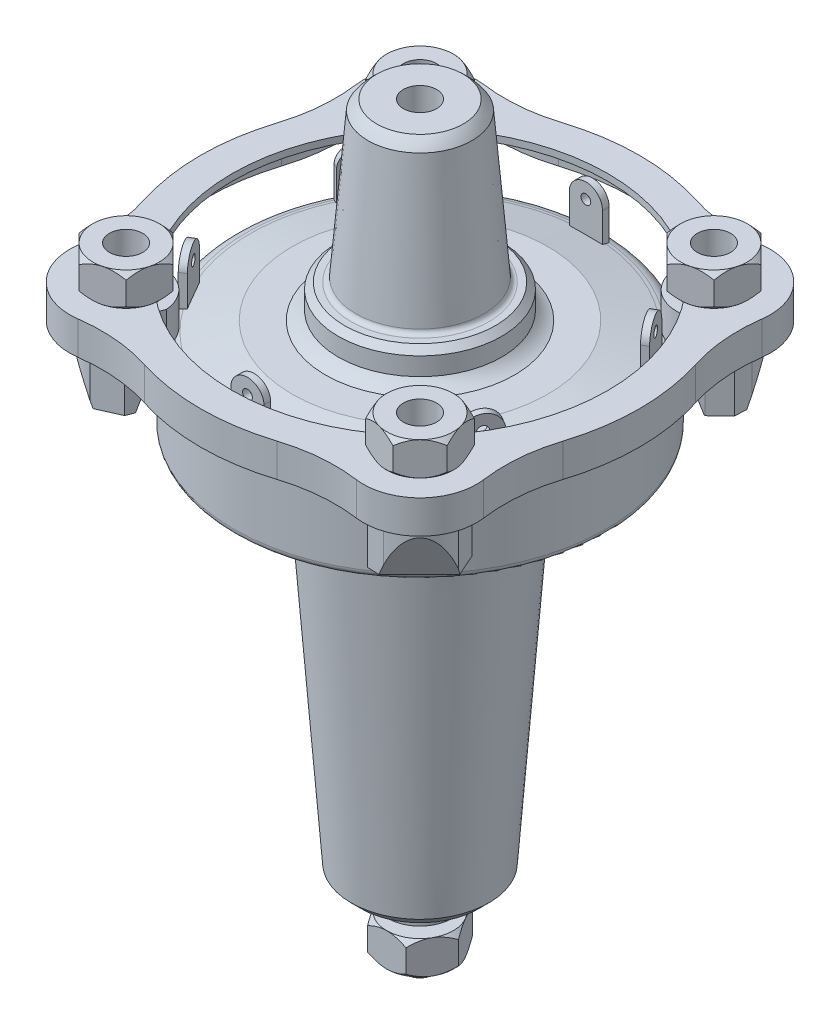
SolidWorks part; units mm, degrees
ref_plane "Front Plane" through (0, 0, 0) normal (0, 0, 1) x (1, 0, 0)
ref_plane "Top Plane" through (0, 0, 0) normal (0, 1, 0) x (1, 0, 0)
ref_plane "Right Plane" through (0, 0, 0) normal (1, 0, 0) x (0, 0, -1)
sketch "Sketch1" plane through (0, 0, 0) normal (0, 0, 1) x (1, 0, 0)
  line L0 (0, 166.4746) -> (0, -166.4746) construction
  line L1 (-56, 2.0022) -> (-56, 20.3181)
  line L2 (-28.0132, -12.6366) -> (-20.7003, -113)
  line L3 (-17.7003, -116) -> (0, -116)
  line L4 (-5.0055, -122.5803) -> (-9.6428, -122.5803) construction
  line L5 (-5.0055, -136) -> (-5.0055, -122.5803) construction
  line L6 (-2.0055, -139) -> (-5.0055, -136) construction
  line L7 (0.0742, -139) -> (-2.0055, -139) construction
  line L8 (-9.6428, -122.5803) -> (-9.6428, -116) construction
  line L9 (-20.7003, -113) -> (-17.7003, -116)
  line L10 (-54.1689, 0) -> (-40.2943, 0)
  line L11 (-38, -8) -> (-33, -8)
  line L12 (-38, -2.0022) -> (-38, -8)
  line L13 (-13.0055, 86) -> (-5.0055, 86)
  line L14 (-19.2424, 39.6846) -> (-15.6526, 83)
  line L15 (-52.1261, 25.194) -> (-51.0561, 25.4408)
  line L16 (-51.0561, 25.4408) -> (-38.4491, 28.3512)
  line L17 (-24.5676, 36.4753) -> (-22.7003, 38.3425)
  line L18 (-38.4491, 28.3512) -> (-28.4491, 28.3512)
  line L19 (-24.5676, 31.062) -> (-24.5676, 36.4753)
  line L20 (-22.7003, 38.3425) -> (-20.7003, 38.3425)
  line L21 (-40.2943, 0) -> (0, 0) construction
  line L22 (-5.0055, -116) -> (-5.0055, 86)
  arc A0 (-38, -2.0022) -> (-40.2943, 0) centre (-40.0021, -1.9808) ccw
  arc A1 (-56, 2.0022) -> (-54.1689, 0) centre (-53.9978, 1.9949) ccw
  arc A2 (-28.0132, -12.6366) -> (-33, -8) centre (-33, -13) ccw
  arc A3 (-52.1261, 25.194) -> (-56, 20.3181) centre (-50.9945, 20.3181) ccw
  arc A4 (-28.4491, 28.3512) -> (-24.5676, 31.062) centre (-31.6492, 37.0674) ccw
  arc A5 (-20.7003, 38.3425) -> (-19.2424, 39.6846) centre (-20.7003, 39.8055) ccw
  arc A6 (-13.0055, 86) -> (-15.6526, 83) centre (-3.4278, 74.881) ccw
  dimension "D11" = 5
  dimension "D13" = 3
  dimension "D16" = 1.4629
  dimension "D20" = 9.2851
  dimension "D1" = 225
  dimension "D2" = 108
  dimension "D3" = 15.6526
  dimension "D4" = 5.0055
  dimension "D5" = 28.3512
  dimension "D6" = 38
  dimension "D7" = 56
  dimension "D8" = 8
  dimension "D9" = 86
  dimension "D10" = 5
  dimension "D12" = 8
  dimension "D14" = 6.5803
  dimension "D15" = 2
  dimension "D17" = 3
  dimension "D18" = 3
  dimension "D19" = 10
  dimension "D21" = 39.6846
  dimension "D22" = 3
  dimension "D23" = 3
revolve "Revolve1" add sketch "Sketch1" angle 360 about L0
sketch "Sketch2" plane through (0, 0, 0) normal (0, 0, 1) x (1, 0, 0)
  line L0 (-9.6428, -116) -> (-9.6428, -122.5803)
  line L1 (-9.6428, -122.5803) -> (-5.0055, -122.5803)
  line L2 (-5.0055, -122.5803) -> (-5.0055, -136)
  line L3 (-5.0055, -136) -> (-4.0044, -140.0739)
  line L4 (-4.0044, -140.0739) -> (0, -140.0739)
  line L5 (0, -140.0739) -> (0, -116)
  line L6 (-9.6428, -116) -> (0, -116)
  line L7 (-17.7003, -116) -> (17.7003, -116) construction
  dimension "D1" = 24.0739
revolve "Revolve2" add sketch "Sketch2" angle 360 about L0
sketch "Sketch3" plane through (0, 28.3512, 0) normal (0, 1, 0) x (1, 0, 0)
  line L0 (0, 0) -> (-54.025, 54.025) construction
  line L1 (0, 0) -> (0, 76.5481) construction
  line L2 (-40.52, 47.5855) -> (-36.6301, 43.0173)
  line L3 (-47.5855, 40.52) -> (-43.3277, 36.2623)
  line L4 (80.1584, 0) -> (-80.1584, 0) construction
  line L5 (-47.5855, -40.52) -> (-43.3277, -36.2623)
  line L6 (-40.52, -47.5855) -> (-36.6301, -43.0173)
  line L7 (0, 0) -> (54.025, 54.025) construction
  line L8 (40.52, -47.5855) -> (36.6301, -43.0173)
  line L9 (47.5855, -40.52) -> (43.3277, -36.2623)
  line L10 (47.5855, 40.52) -> (43.3277, 36.2623)
  line L11 (40.52, 47.5855) -> (36.6301, 43.0173)
  arc A0 (-62.9108, 19.9557) -> (-62.9108, -19.9557) centre (0, 0) ccw
  arc A1 (-43.3277, 36.2623) -> (-43.3277, -36.2623) centre (0, 0) ccw
  arc A2 (62.5, 0) -> (-62.5, 0) centre (0, 0) ccw construction
  arc A3 (-40.52, 47.5855) -> (-47.5855, 40.52) centre (-44.1942, 44.1942) ccw
  arc A4 (-41.88, 61.0359) -> (-61.0359, 41.88) centre (-44.1942, 44.1942) ccw
  circle A5 centre (-44.1942, 44.1942) radius 5 construction
  circle A6 centre (-44.1942, 44.1942) radius 17 construction
  arc A7 (19.9557, 62.9108) -> (-19.9557, 62.9108) centre (0, 0) ccw
  arc A8 (36.6301, 43.0173) -> (-36.6301, 43.0173) centre (0, 0) ccw
  arc A9 (-41.88, 61.0359) -> (-19.9557, 62.9108) centre (-35.0737, 110.5705) ccw
  arc A10 (-61.0359, 41.88) -> (-62.9108, 19.9557) centre (-110.5705, 35.0737) cw
  arc A11 (19.9557, -62.9108) -> (-19.9557, -62.9108) centre (0, 0) cw
  arc A12 (36.6301, -43.0173) -> (-36.6301, -43.0173) centre (0, 0) cw
  arc A13 (-61.0359, -41.88) -> (-62.9108, -19.9557) centre (-110.5705, -35.0737) ccw
  arc A14 (-41.88, -61.0359) -> (-19.9557, -62.9108) centre (-35.0737, -110.5705) cw
  arc A15 (-41.88, -61.0359) -> (-61.0359, -41.88) centre (-44.1942, -44.1942) cw
  arc A16 (-40.52, -47.5855) -> (-47.5855, -40.52) centre (-44.1942, -44.1942) cw
  arc A17 (40.52, -47.5855) -> (47.5855, -40.52) centre (44.1942, -44.1942) ccw
  arc A18 (41.88, -61.0359) -> (61.0359, -41.88) centre (44.1942, -44.1942) ccw
  arc A19 (41.88, -61.0359) -> (19.9557, -62.9108) centre (35.0737, -110.5705) ccw
  arc A20 (61.0359, -41.88) -> (62.9108, -19.9557) centre (110.5705, -35.0737) cw
  arc A21 (61.0359, 41.88) -> (62.9108, 19.9557) centre (110.5705, 35.0737) ccw
  arc A22 (41.88, 61.0359) -> (19.9557, 62.9108) centre (35.0737, 110.5705) cw
  arc A23 (41.88, 61.0359) -> (61.0359, 41.88) centre (44.1942, 44.1942) cw
  arc A24 (40.52, 47.5855) -> (47.5855, 40.52) centre (44.1942, 44.1942) cw
  arc A25 (43.3277, 36.2623) -> (43.3277, -36.2623) centre (0, 0) cw
  arc A26 (62.9108, 19.9557) -> (62.9108, -19.9557) centre (0, 0) cw
  dimension "D1" = 132
  dimension "D2" = 113
  dimension "D3" = 125
  dimension "D5" = 10
  dimension "D7" = 50
  dimension "D4" = 45
  dimension "D6" = 12
extrude "Boss-Extrude1" add sketch "Sketch3" along normal blind 10 separate body
shell "Shell1" thickness 2
sketch "Sketch5" plane through (0, 0, 0) normal (0, 1, 0) x (1, 0, 0)
  line L0 (-56.215, 56.215) -> (56.215, -56.215) construction
  arc A0 (-41.88, 61.0359) -> (-61.0359, 41.88) centre (-44.1942, 44.1942) ccw construction
  arc A1 (41.88, -61.0359) -> (61.0359, -41.88) centre (44.1942, -44.1942) ccw construction
ref_plane "Plane2" through (0, 0, 0) normal (-0.7071, 0, 0.7071) x (0.7071, 0, 0.7071)
sketch "Sketch6" plane through (0, 36.3512, 0) normal (0, -1, 0) x (1, 0, 0)
  line L0 (-44.4685, -55.424) -> (-39.4441, -55.1901)
  line L1 (-39.4441, -55.1901) -> (-35.0009, -50.6492)
  line L2 (-55.4219, -43.8429) -> (-52.2302, -36.6333)
  line L3 (-52.2302, -36.6333) -> (-43.2487, -33.0009)
  circle A0 centre (-44.1942, -44.1942) radius 6
  arc A1 (-35.0009, -50.6492) -> (-43.2487, -33.0009) centre (-44.1942, -44.1942) ccw
  arc A2 (-55.4219, -43.8429) -> (-44.4685, -55.424) centre (-44.1942, -44.1942) ccw
  line M17 (-47.5855, -40.52) -> (-43.3277, -36.2623)
  arc M18 (-43.3277, -36.2623) -> (-43.3277, 36.2623) centre (0, 0) cw
  arc M30 (36.6301, -43.0173) -> (-36.6301, -43.0173) centre (0, 0) cw
  line M31 (-36.6301, -43.0173) -> (-40.52, -47.5855)
  dimension "D1" = 12
extrude "Boss-Extrude2" add sketch "Sketch6" along normal blind 25 separate body contours L2 A2 L0 L1 A1 A0 L3 M30 M31 M17 M18 | A1 L3 A0 M30 M18 M17 M31
sketch "Sketch9" plane through (0, 0, 0) normal (-0.7071, 0, 0.7071) x (0.7071, 0, 0.7071)
  line L0 (-65.5502, -3.0446) -> (-56.4356, 22.8867)
  line L1 (-50.7439, 26.5641) -> (-50.7439, -3.0446)
  line L2 (-50.7439, -3.0446) -> (-65.5502, -3.0446)
  arc A0 (-56.4356, 22.8867) -> (-50.7439, 26.5641) centre (-51.1323, 20.9219) cw
extrude "Cut-Extrude1" cut sketch "Sketch9" against normal up to next and the other way up to next
sketch "Sketch18" plane through (0, 0, 0) normal (-0.7071, 0, 0.7071) x (0.7071, 0, 0.7071)
  line L0 (-73.7332, 23.8512) -> (-69.328, 10.7679)
  line L1 (-73.7332, 36.3512) -> (-73.7332, 11.3512) construction
  line L2 (-73.7332, 23.8512) -> (-73.7332, 10.7679)
  line L6 (-73.7332, 10.7679) -> (-69.328, 10.7679)
extrude "Cut-Extrude2" cut sketch "Sketch18" against normal blind 25 and the other way blind 25
sketch "Sketch11" plane through (0, 0, 0) normal (0, -1, 0) x (1, 0, 0)
  circle A0 centre (-44.1942, -44.1942) radius 5
  dimension "D1" = 10
extrude "Boss-Extrude4" add sketch "Sketch11" against normal blind 55 from offset 4 separate body
sketch "Sketch12" plane through (0, 38.3512, 0) normal (0, 1, 0) x (1, 0, 0)
  line L0 (-51.2652, 51.2652) -> (-37.1231, 37.1231) construction
  line L1 (-47.1828, 55.3477) -> (-55.3477, 47.1828)
  line L2 (-55.3477, 47.1828) -> (-52.3591, 36.0292)
  line L3 (-52.3591, 36.0292) -> (-41.2056, 33.0406)
  line L4 (-41.2056, 33.0406) -> (-33.0406, 41.2056)
  line L5 (-33.0406, 41.2056) -> (-36.0292, 52.3591)
  line L6 (-36.0292, 52.3591) -> (-47.1828, 55.3477)
  line L7 (-61.8365, 61.8365) -> (61.8365, -61.8365) construction
  circle A0 centre (-44.1942, 44.1942) radius 10 construction
  circle A1 centre (-44.1942, 44.1942) radius 5
  dimension "D1" = 20
extrude "Boss-Extrude5" add sketch "Sketch12" along normal blind 10 from offset 0.2 separate body
sketch "Sketch15" plane through (0, 0, 0) normal (-0.7071, 0, 0.7071) x (0.7071, 0, 0.7071)
  line L0 (-75.3371, 48.5512) -> (-72.5, 48.5512)
  line L1 (-75.3371, 48.5512) -> (-75.3371, 45.7141)
  line L2 (-72.5, 48.5512) -> (-75.3371, 45.7141)
  line L3 (-62.5, 51) -> (-62.5, 58.9815) construction
  line L4 (-57.5, 51) -> (-67.5, 51) construction
  line L5 (-72.5, 38.5512) -> (-75.3371, 38.5512)
  line L6 (-75.3371, 38.5512) -> (-75.3371, 41.3882)
  line L7 (-75.3371, 41.3882) -> (-72.5, 38.5512)
revolve "Cut-Revolve6" cut sketch "Sketch15" angle 360 about L3
pattern_circular "CirPattern2" count 4 over 360 about axis through (0, 0, 0) along (0, 1, 0) of bodies 113 122 105 110
sketch "Sketch16" plane through (0, -122.5803, 0) normal (0, -1, 0) x (1, 0, 0)
  line L1 (-5.7735, 10) -> (-11.547, 0)
  line L2 (-11.547, 0) -> (-5.7735, -10)
  line L3 (-5.7735, -10) -> (5.7735, -10)
  line L4 (5.7735, -10) -> (11.547, 0)
  line L5 (11.547, 0) -> (5.7735, 10)
  line L6 (5.7735, 10) -> (-5.7735, 10)
  circle A0 centre (0, 0) radius 10 construction
  circle A2 centre (0, 0) radius 5
  dimension "D1" = 20
  dimension "D2" = 10
extrude "Boss-Extrude6" add sketch "Sketch16" along normal blind 10 from offset 3 separate body
sketch "Sketch17" plane through (0, 0, 0) normal (1, 0, 0) x (0, 0, -1)
  line L0 (-10, -125.5803) -> (-13, -125.5803)
  line L1 (-13, -125.5803) -> (-13, -128.5803)
  line L2 (-13, -128.5803) -> (-10, -125.5803)
  line L3 (-10, -135.5803) -> (-13, -135.5803)
  line L4 (-13, -135.5803) -> (-13, -132.5803)
  line L5 (-13, -132.5803) -> (-10, -135.5803)
  line L6 (0, -140.0739) -> (0, -121.7016) construction
  line L7 (-4.0044, -140.0739) -> (4.0044, -140.0739) construction
  dimension "D1" = 3
  dimension "D2" = 3
revolve "Cut-Revolve7" cut sketch "Sketch17" angle 360 about L6
sketch "Sketch19" plane through (0, 0, 0) normal (0, 1, 0) x (1, 0, 0)
  line L0 (0, 0) -> (0, 58.9558) construction
  line L1 (-5, 51.8857) -> (5, 51.8857)
  line L2 (-5, 51.8857) -> (-5, 49.8857)
  line L3 (-5, 49.8857) -> (5, 49.8857)
  line L4 (5, 51.8857) -> (5, 49.8857)
  circle A0 centre (0, 0) radius 52.1261 construction
  dimension "D1" = 2
  dimension "D2" = 10
extrude "Boss-Extrude7" add sketch "Sketch19" along normal blind 17 from offset 23 separate body
sketch "Sketch20" plane through (0, 0, -49.8857) normal (0, 0, 1) x (1, 0, 0)
  line L0 (-5, 40) -> (-5, 23) construction
  line L2 (5, 34.4872) -> (5, 40)
  line L3 (5, 40) -> (-5, 40)
  line L4 (-5, 40) -> (5, 40) construction
  line L5 (-5, 40) -> (-5, 34.8213)
  line L6 (5, 40) -> (5, 23) construction
  arc A0 (-5, 34.8213) -> (5, 34.4872) centre (-0.0056, 34.4872) cw
  dimension "D1" = 5.0056
extrude "Cut-Extrude3" cut sketch "Sketch20" against normal blind 3
sketch "Sketch21" plane through (0, 0, -49.8857) normal (0, 0, 1) x (1, 0, 0)
  circle A0 centre (0, 34.9194) radius 1.4684
extrude "Cut-Extrude4" cut sketch "Sketch21" against normal up to next (2 mm away)
pattern_circular "CirPattern3" count 6 over 360 about axis through (0, 0, 0) along (0, 1, 0) of bodies 125
sketch "Sketch22" plane through (0, 51, 0) normal (0, 1, 0) x (1, 0, 0)
  circle A1 centre (-44.1942, 44.1942) radius 5
  circle A2 centre (-44.1942, 44.1942) radius 5
  dimension "D1" = 0
extrude "Cut-Extrude5" cut sketch "Sketch22" against normal up to surface (55 mm away) up to face at (-44.1942, -4, -49.1942)
